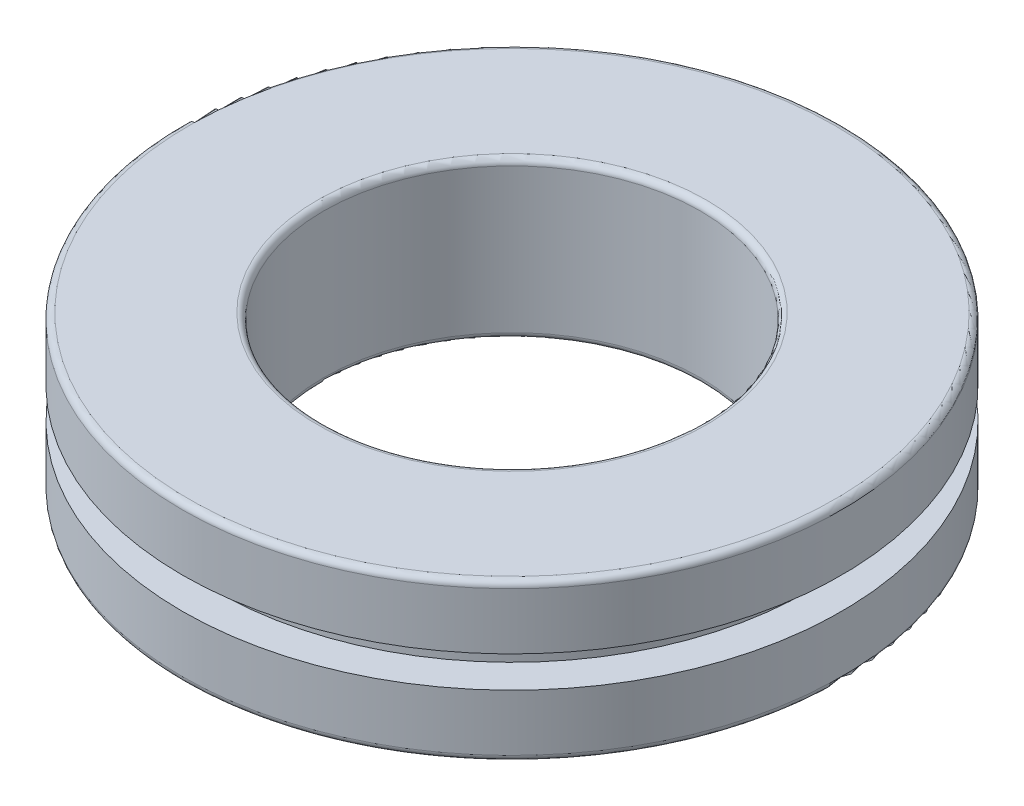
SolidWorks part; units mm, degrees
material "Nickel"
ref_plane "Front Plane" through (0, 0, 0) normal (0, 0, 1) x (1, 0, 0)
ref_plane "Top Plane" through (0, 0, 0) normal (0, 1, 0) x (1, 0, 0)
ref_plane "Right Plane" through (0, 0, 0) normal (1, 0, 0) x (0, 0, -1)
sketch "Sketch1" plane through (0, 0, 0) normal (0, 0, 1) x (1, 0, 0)
  line L0 (6, 0.2) -> (6, 4.8)
  line L1 (6.2, 5) -> (10.3, 5)
  line L2 (10.5, 4.8) -> (10.5, 3)
  line L3 (10.5, 3) -> (9.4119, 3)
  line L4 (9.4119, 3) -> (9.4119, 2)
  line L5 (9.4119, 2) -> (10.5, 2)
  line L6 (10.5, 2) -> (10.5, 0.2)
  line L7 (10.3, 0) -> (6.2, 0)
  line L8 (0, 0) -> (0, 5) construction
  arc A0 (10.5, 0.2) -> (10.3, 0) centre (10.3, 0.2) cw
  arc A1 (10.3, 5) -> (10.5, 4.8) centre (10.3, 4.8) cw
  arc A2 (6, 0.2) -> (6.2, 0) centre (6.2, 0.2) ccw
  arc A3 (6, 4.8) -> (6.2, 5) centre (6.2, 4.8) cw
  point P13 (10.5, 0)
  point P16 (10.5, 5)
  dimension "D6" = 0.2
  dimension "D1" = 5
  dimension "D2" = 6
  dimension "D3" = 10.5
  dimension "D4" = 2
  dimension "D5" = 2
revolve "Revolve1" add sketch "Sketch1" angle 360 about L8
